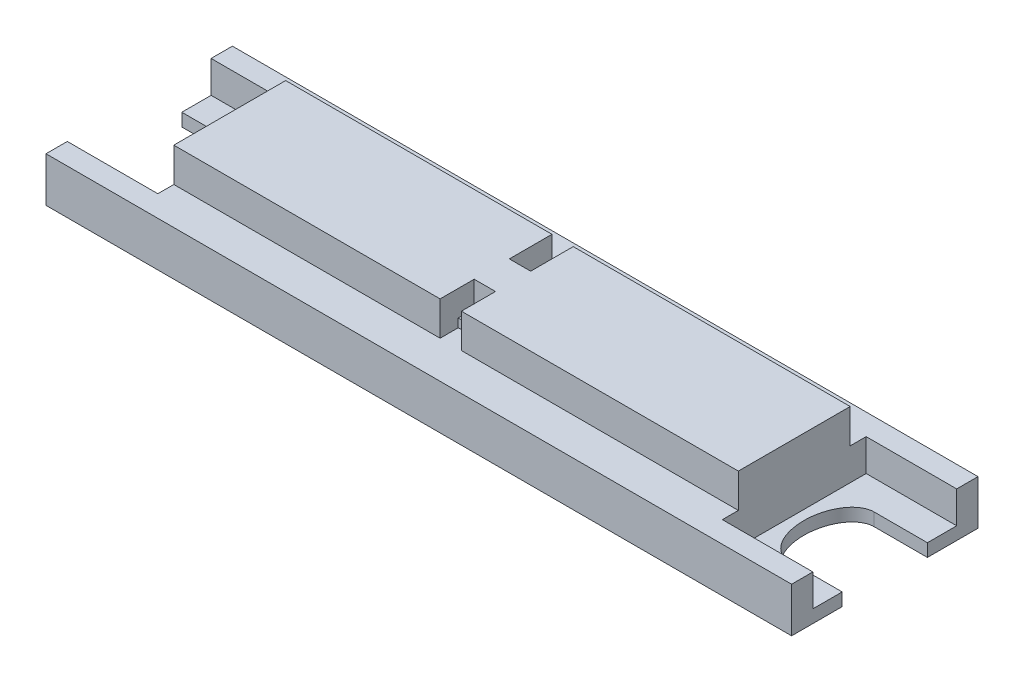
SolidWorks part; units mm, degrees
ref_plane "Alzado" through (0, 0, 0) normal (0, 0, 1) x (1, 0, 0)
ref_plane "Planta" through (0, 0, 0) normal (0, 1, 0) x (1, 0, 0)
ref_plane "Vista lateral" through (0, 0, 0) normal (1, 0, 0) x (0, 0, -1)
sketch "Croquis1" plane through (0, 0, 0) normal (0, 1, 0) x (1, 0, 0)
  line L1 (-32.7297, 4.4459) -> (37.2703, 4.4459)
  line L2 (-32.7297, 4.4459) -> (-32.7297, -13.0541)
  line L3 (-32.7297, -13.0541) -> (37.2703, -13.0541)
  line L4 (37.2703, 4.4459) -> (37.2703, -13.0541)
  dimension "D1" = 70
  dimension "D2" = 17.5
extrude "Saliente-Extruir1" add sketch "Croquis1" along normal blind 4.2
sketch "Croquis2" plane through (0, 4.2, 0) normal (0, 1, 0) x (1, 0, 0)
  line L0 (37.2703, -13.0541) -> (37.2703, 4.4459) construction
  line L1 (37.2703, 2.4459) -> (28.7703, 2.4459)
  line L2 (37.2703, 2.4459) -> (37.2703, -11.0541)
  line L3 (37.2703, -11.0541) -> (28.7703, -11.0541)
  line L4 (28.7703, 2.4459) -> (28.7703, -11.0541)
  line L5 (37.2703, 4.4459) -> (-32.7297, 4.4459) construction
  line L6 (-32.7297, -13.0541) -> (37.2703, -13.0541) construction
  line L7 (-32.7297, 4.4459) -> (-32.7297, -13.0541) construction
  line L8 (-32.7297, 2.4459) -> (-24.2297, 2.4459)
  line L9 (-32.7297, 2.4459) -> (-32.7297, -11.0541)
  line L10 (-32.7297, -11.0541) -> (-24.2297, -11.0541)
  line L11 (-24.2297, 2.4459) -> (-24.2297, -11.0541)
  dimension "D1" = 2
  dimension "D2" = 2
  dimension "D3" = 8.5
  dimension "D4" = 8.5
  dimension "D5" = 2
  dimension "D6" = 2
extrude "Cortar-Extruir1" cut sketch "Croquis2" against normal blind 3
sketch "Croquis3" plane through (0, 1.2, 0) normal (0, 1, 0) x (1, 0, 0)
  line L0 (37.2703, -0.3041) -> (32.2703, -0.3041)
  line L1 (37.2703, -11.0541) -> (37.2703, 2.4459) construction
  line L2 (37.2703, -8.3041) -> (32.2703, -8.3041)
  line L3 (28.7703, -11.0541) -> (37.2703, -11.0541) construction
  line L4 (37.2703, 2.4459) -> (28.7703, 2.4459) construction
  line L5 (32.2703, -0.3041) -> (32.2703, -8.3041) construction
  line L6 (28.7703, 2.4459) -> (28.7703, -11.0541) construction
  line L7 (37.2703, -0.3041) -> (37.2703, -8.3041)
  line L8 (-32.7297, -0.3041) -> (-27.7297, -0.3041)
  line L9 (-32.7297, 2.4459) -> (-32.7297, -11.0541) construction
  line L10 (-32.7297, -8.3041) -> (-27.7297, -8.3041)
  line L11 (-32.7297, -0.3041) -> (-32.7297, -8.3041)
  line L12 (-32.7297, -11.0541) -> (-24.2297, -11.0541) construction
  line L13 (-24.2297, 2.4459) -> (-32.7297, 2.4459) construction
  line L14 (-27.7297, -0.3041) -> (-27.7297, -8.3041) construction
  line L15 (-24.2297, -11.0541) -> (-24.2297, 2.4459) construction
  ellipse E0 centre (32.2703, -4.3041) end of major axis (32.2703, -0.3041) minor radius 2.6 (29.7703, -5.4027) -> (32.2703, -0.3041) cw
  ellipse E1 centre (32.2703, -4.3041) end of major axis (32.2703, -8.3041) minor radius 2.6 (29.7703, -5.4027) -> (32.2703, -8.3041) ccw
  ellipse E2 centre (-27.7297, -4.3041) end of major axis (-27.7297, -0.3041) minor radius 2.5 (-25.2297, -4.3041) -> (-27.7297, -8.3041) cw
  ellipse E3 centre (-27.7297, -4.3041) end of major axis (-27.7297, -0.3041) minor radius 2.5 (-25.2297, -4.3041) -> (-27.7297, -0.3041) ccw
  point P10 (29.7703, -5.4027)
  point P33 (-25.2297, -4.3041)
  dimension "D1" = 2.75
  dimension "D2" = 2.75
  dimension "D3" = 5
  dimension "D4" = 5
  dimension "D5" = 1
  dimension "D6" = 5
  dimension "D7" = 5
  dimension "D8" = 2.75
  dimension "D9" = 2.75
  dimension "D10" = 1
extrude "Cortar-Extruir2" cut sketch "Croquis3" against normal through all
sketch "Croquis4" plane through (0, 4.2, 0) normal (0, 1, 0) x (1, 0, 0)
  line L0 (-24.2297, -11.0541) -> (-24.2297, 2.4459) construction
  line L1 (-24.2297, 0.9459) -> (0.7703, 0.9459)
  line L2 (-24.2297, 0.9459) -> (-24.2297, -9.5541)
  line L3 (-24.2297, -9.5541) -> (0.7703, -9.5541)
  line L5 (37.2703, 4.4459) -> (-32.7297, 4.4459) construction
  line L6 (-32.7297, -13.0541) -> (37.2703, -13.0541) construction
  line L7 (0.7703, 0.9459) -> (0.7703, -3.0541)
  line L8 (0.7703, -9.5541) -> (0.7703, -6.3541)
  line L9 (0.7703, -3.0541) -> (2.7703, -3.0541)
  line L10 (0.7703, -6.3541) -> (2.7703, -6.3541)
  line L11 (2.7703, -3.0541) -> (2.7703, 0.9459)
  line L12 (2.7703, 0.9459) -> (28.7703, 0.9459)
  line L13 (28.7703, 2.4459) -> (28.7703, -11.0541) construction
  line L14 (28.7703, 0.9459) -> (28.7703, -9.5541)
  line L15 (28.7703, 2.4459) -> (28.7703, -11.0541) construction
  line L16 (28.7703, -9.5541) -> (2.7703, -9.5541)
  line L17 (2.7703, -9.5541) -> (2.7703, -6.3541)
  dimension "D1" = 3.5
  dimension "D2" = 3.5
  dimension "D3" = 4
  dimension "D4" = 3.2
  dimension "D5" = 2
  dimension "D6" = 2
extrude "Saliente-Extruir2" add sketch "Croquis4" along normal blind 3.2
sketch "Croquis5" plane through (0, 0, 0) normal (0, -1, 0) x (1, 0, 0)
  line L0 (-25.2741, 3.5541) -> (-21.2741, 3.5541) construction
  line L1 (-14.7741, 10.0541) -> (-14.7741, 13.0541) construction
  line L2 (-32.7297, 13.0541) -> (37.2703, 13.0541) construction
  line L3 (29.7164, 3.5541) -> (25.7164, 3.5541) construction
  line L4 (19.2164, 10.0541) -> (19.2164, 13.0541) construction
  circle A0 centre (-14.7741, 3.5541) radius 6.5
  circle A1 centre (19.2164, 3.5541) radius 6.5
  ellipse E0 centre (-27.7297, 4.3041) end of major axis (-27.7297, 0.3041) minor radius 2.5 (-27.7297, 0.3041) -> (-27.7297, 8.3041) ccw construction
  ellipse E2 centre (32.2703, 4.3041) end of major axis (32.2703, 0.3041) minor radius 2.6 (32.2703, 8.3041) -> (32.2703, 0.3041) ccw construction
  dimension "D1" = 13
  dimension "D4" = 13
  dimension "D2" = 4
  dimension "D3" = 3
  dimension "D5" = 4
  dimension "D6" = 3
extrude "Cortar-Extruir3" cut sketch "Croquis5" against normal blind 4
sketch "Croquis6" plane through (0, 4, 0) normal (0, -1, 0) x (1, 0, 0)
  line L0 (-19.0741, 3.5541) -> (-21.2741, 3.5541) construction
  line L1 (-19.0741, 6.8041) -> (-15.5741, 6.8041)
  line L2 (-19.0741, 6.8041) -> (-19.0741, 0.3041)
  line L3 (-19.0741, 0.3041) -> (-15.5741, 0.3041)
  line L4 (-15.5741, 6.8041) -> (-15.5741, 0.3041)
  line L5 (-13.9741, 6.8041) -> (-10.4741, 6.8041)
  line L6 (-13.9741, 6.8041) -> (-13.9741, 0.3041)
  line L7 (-13.9741, 0.3041) -> (-10.4741, 0.3041)
  line L8 (-10.4741, 6.8041) -> (-10.4741, 0.3041)
  line L9 (-10.4741, 3.5541) -> (-8.2741, 3.5541) construction
  line L10 (-15.5741, 6.8041) -> (-13.9741, 6.8041) construction
  line L11 (14.9629, 3.2932) -> (12.7629, 3.2932) construction
  line L12 (14.9629, 6.5432) -> (18.4629, 6.5432)
  line L13 (14.9629, 6.5432) -> (14.9629, 0.0432)
  line L14 (14.9629, 0.0432) -> (18.4629, 0.0432)
  line L15 (18.4629, 6.5432) -> (18.4629, 0.0432)
  line L16 (20.0629, 6.5432) -> (23.5629, 6.5432)
  line L17 (20.0629, 6.5432) -> (20.0629, 0.0432)
  line L18 (20.0629, 0.0432) -> (23.5629, 0.0432)
  line L19 (23.5629, 6.5432) -> (23.5629, 0.0432)
  line L20 (23.5629, 3.2932) -> (25.7629, 3.2932) construction
  line L21 (18.4629, 6.5432) -> (20.0629, 6.5432) construction
  circle A0 centre (-14.7741, 3.5541) radius 6.5 construction
  circle A1 centre (-14.7741, 3.5541) radius 6.5 construction
  dimension "D1" = 3.5
  dimension "D2" = 3.5
  dimension "D3" = 2.2
  dimension "D4" = 6.5
  dimension "D5" = 90
  dimension "D6" = 2.2
  dimension "D7" = 90
  dimension "D8" = 6.5
  dimension "D9" = 3.5
  dimension "D10" = 3.5
  dimension "D11" = 2.2
  dimension "D12" = 6.5
  dimension "D13" = 90
  dimension "D14" = 2.2
  dimension "D15" = 90
  dimension "D16" = 6.5
extrude "Cortar-Extruir4" cut sketch "Croquis6" against normal blind 1
sketch "Croquis7" plane through (0, 0, 0) normal (0, -1, 0) x (1, 0, 0)
  line L0 (37.2703, -4.4459) -> (-32.7297, -4.4459) construction
  line L1 (-5.7081, 0.7541) -> (8.2919, 0.7541)
  line L2 (-5.7081, 0.7541) -> (-5.7081, -1.2459)
  line L3 (-5.7081, -1.2459) -> (8.2919, -1.2459)
  line L4 (8.2919, 0.7541) -> (8.2919, -1.2459)
  line L5 (-5.7081, 0.7541) -> (-8.9081, 0.7541) construction
  line L6 (-5.7081, 9.8541) -> (-5.7081, 13.0541) construction
  line L7 (-5.7081, 9.8541) -> (8.2919, 9.8541)
  line L8 (-5.7081, 9.8541) -> (-5.7081, 7.8541)
  line L9 (-5.7081, 7.8541) -> (8.2919, 7.8541)
  line L10 (8.2919, 9.8541) -> (8.2919, 7.8541)
  line L11 (-32.7297, 13.0541) -> (37.2703, 13.0541) construction
  line L12 (-5.7081, 7.8541) -> (-9.8996, 7.8541) construction
  circle A0 centre (-14.7741, 3.5541) radius 6.5 construction
  circle A1 centre (-14.7741, 3.5541) radius 6.5 construction
  dimension "D1" = 3.2
  dimension "D2" = 3.2
  dimension "D3" = 14
  dimension "D4" = 2
  dimension "D5" = 2
  dimension "D6" = 14
  dimension "D7" = 3.2
extrude "Cortar-Extruir5" cut sketch "Croquis7" against normal blind 1
sketch "Croquis8" plane through (0, 0, 0) normal (0, -1, 0) x (1, 0, 0)
  line L0 (-5.7081, 7.8541) -> (-5.7081, 0.7541)
  line L1 (-5.7081, 0.7541) -> (8.2919, 0.7541)
  line L2 (-5.7081, 7.8541) -> (8.2919, 7.8541)
  line L3 (8.2919, 0.7541) -> (12.2919, 0.7541)
  line L4 (8.2919, 7.8541) -> (12.2919, 7.8541)
  line L5 (12.2919, 7.8541) -> (12.2919, 0.7541) construction
  line L6 (12.2919, 4.3041) -> (11.2919, 4.3041) construction
  ellipse E0 centre (12.2919, 4.3041) end of major axis (12.2919, 7.8541) minor radius 1 (11.2919, 4.3041) -> (12.2919, 0.7541) ccw
  ellipse E1 centre (12.2919, 4.3041) end of major axis (12.2919, 7.8541) minor radius 1 (11.2919, 4.3041) -> (12.2919, 7.8541) cw
  dimension "D1" = 4
  dimension "D2" = 4
  dimension "D3" = 1
extrude "Cortar-Extruir6" cut sketch "Croquis8" against normal blind 4
sketch "Croquis9" plane through (0, 4, 0) normal (0, -1, 0) x (1, 0, 0)
  line L0 (12.2919, 7.8541) -> (-5.7081, 7.8541) construction
  line L1 (-1.9972, 7.8541) -> (1.4919, 7.8541)
  line L2 (-1.9972, 7.8541) -> (-1.9972, 0.7541)
  line L3 (-1.9972, 0.7541) -> (1.4919, 0.7541)
  line L4 (1.4919, 7.8541) -> (1.4919, 0.7541)
  line L5 (-5.7081, 0.7541) -> (12.2919, 0.7541) construction
  line L6 (1.4919, 4.3041) -> (11.2919, 4.3041) construction
  ellipse E0 centre (12.2919, 4.3041) end of major axis (12.2919, 7.8541) minor radius 1 (12.2919, 7.8541) -> (12.2919, 0.7541) ccw construction
  ellipse E1 centre (12.2919, 4.3041) end of major axis (12.2919, 7.8541) minor radius 1 (12.2919, 7.8541) -> (12.2919, 0.7541) ccw construction
extrude "Saliente-Extruir3" add sketch "Croquis9" against normal blind 1 and the other way blind 2
